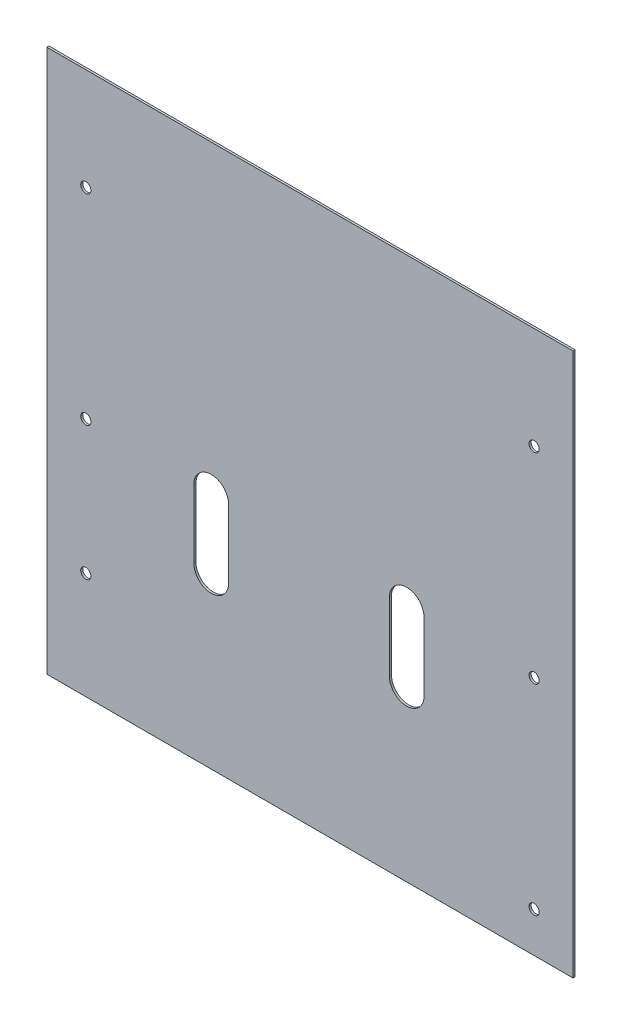
SolidWorks part; units mm, degrees
ref_plane "Front Plane" through (0, 0, 0) normal (0, 0, 1) x (1, 0, 0)
ref_plane "Top Plane" through (0, 0, 0) normal (0, 1, 0) x (1, 0, 0)
ref_plane "Right Plane" through (0, 0, 0) normal (1, 0, 0) x (0, 0, -1)
sketch "Sketch1" plane through (0, 0, 0) normal (0, 0, -1) x (1, 0, 0)
  line L1 (-203.2, 237) -> (-6.35, 237)
  line L2 (-203.2, 237) -> (-203.2, 33.8)
  line L3 (-203.2, 33.8) -> (-6.35, 33.8)
  line L4 (-6.35, 237) -> (-6.35, 33.8)
  dimension "D2" = 196.85
  dimension "D3" = 203.2
extrude "Boss-Extrude1" add sketch "Sketch1" along normal blind 0.7747
sketch "Sketch2" plane through (0, 0, -0.7747) normal (0, 0, -1) x (1, 0, 0)
  line L0 (-141.7213, 180) -> (-141.7213, 141.5) construction
  line L1 (-6.35, 237) -> (-203.2, 237) construction
  line L2 (-141.7213, 180) -> (-141.7213, 237) construction
  line L3 (-141.7213, 173.5) -> (-141.7213, 148) construction
  line L6 (-135.2213, 173.5) -> (-135.2213, 148)
  line L7 (-148.2213, 173.5) -> (-148.2213, 148)
  line L8 (-141.7213, 160.75) -> (-203.2, 160.75) construction
  line L9 (-203.2, 237) -> (-203.2, 33.8) construction
  line L10 (-68.5693, 180) -> (-68.5693, 141.5) construction
  line L11 (-68.5693, 180) -> (-68.5693, 237) construction
  line L12 (-68.5693, 173.5) -> (-68.5693, 148) construction
  line L15 (-141.7213, 160.75) -> (-68.5693, 160.75) construction
  line L16 (-62.0693, 173.5) -> (-62.0693, 148)
  line L17 (-75.0693, 173.5) -> (-75.0693, 148)
  arc A2 (-135.2213, 173.5) -> (-148.2213, 173.5) centre (-141.7213, 173.5) ccw
  arc A3 (-148.2213, 148) -> (-135.2213, 148) centre (-141.7213, 148) ccw
  arc A6 (-62.0693, 173.5) -> (-75.0693, 173.5) centre (-68.5693, 173.5) ccw
  arc A7 (-75.0693, 148) -> (-62.0693, 148) centre (-68.5693, 148) ccw
  point P5 (-141.7213, 160.75)
  point P18 (-68.5693, 160.75)
  dimension "D4" = 6.5
  dimension "D6" = 57
  dimension "D5" = 6.5
  dimension "D1" = 73.152
  dimension "D2" = 57
  dimension "D3" = 38.5
  dimension "D8" = 38.5
extrude "Cut-Extrude7" cut sketch "Sketch2" against normal through all
ref_plane "Plane1" through (-104.775, 0, 0) normal (1, 0, 0) x (0, 0, -1)
sketch "Sketch4" plane through (0, 0, 0) normal (0, 0, 1) x (1, 0, 0)
  line L0 (-203.2, -33.8) -> (-6.35, -33.8) construction
  line L1 (-6.35, -33.8) -> (-203.2, -33.8)
  line L2 (-6.35, -33.8) -> (-6.35, -34.4096)
  line L3 (-6.35, -34.4096) -> (-203.2, -34.4096)
  line L4 (-203.2, -33.8) -> (-203.2, -34.4096)
  line L5 (-6.35, -237) -> (-6.35, 2) construction
  line L6 (-203.2, 2) -> (-203.2, -237) construction
  dimension "D1" = 0.6096
extrude "Boss-Extrude2" add sketch "Sketch4" along normal blind 12
sketch "Sketch8" plane through (0, 0, -0.7747) normal (0, 0, -1) x (-1, 0, 0)
  circle A0 centre (185.47, -222) radius 3.75
  circle A1 centre (185.47, -197) radius 3.75
  circle A2 centre (185.47, -172) radius 3.75
  circle A3 centre (185.47, -147) radius 3.75
  circle A4 centre (185.47, -122) radius 3.75
  circle A5 centre (185.47, -97) radius 3.75
  dimension "D1" = 7.5
sketch "Sketch13" plane through (0, 0, 12) normal (0, 0, 1) x (1, 0, 0)
  line L1 (-6.35, -34.4096) -> (-203.2, -34.4096)
  line L2 (-6.35, -34.4096) -> (-6.35, -33.8)
  line L3 (-6.35, -33.8) -> (-203.2, -33.8)
  line L4 (-203.2, -34.4096) -> (-203.2, -33.8)
sketch "Sketch14" plane through (0, 0, 0) normal (0, 0, 1) x (1, 0, 0)
  line L0 (-6.35, -34.4096) -> (-6.35, -237) construction
  line L1 (-6.35, -59.904) -> (-203.2, -59.904)
  line L2 (-6.35, -59.904) -> (-6.35, -47.966)
  line L3 (-6.35, -47.966) -> (-203.2, -47.966)
  line L4 (-203.2, -59.904) -> (-203.2, -47.966)
  line L5 (-203.2, -237) -> (-203.2, -34.4096) construction
  dimension "D1" = 11.938
extrude "Boss-Extrude3" add sketch "Sketch14" against normal up to surface (0.7747 mm away) up to face at (-141.7213, -160.75, -0.7747)
extrude "Cut-Extrude9" cut sketch "Sketch13" against normal up to surface (12 mm away) up to face at (-68.5693, -160.75, 0)
hole_wizard "CSK for M3 Flat Head Machine Screw3" positions "Sketch15" profile "Sketch16" tap size "M4x0.7" standard "ANSI Metric" end condition through all
sketch "Sketch15" plane through (0, 0, 0) normal (0, 0, 1) x (1, 0, 0)
  point P18 (-188.645, -72)
  point P21 (-188.645, -222)
  point P24 (-188.645, -197)
  point P27 (-188.645, -172)
  point P30 (-188.645, -147)
  point P33 (-188.645, -122)
  point P36 (-188.645, -97)
  point P39 (-188.645, -72)
sketch "Sketch16" plane through (-188.645, -72, 0) normal (1, 0, 0) x (0, -1, 0)
  line L0 (0, 0) -> (0, 0.7747)
  line L1 (0, 0.7747) -> (1.905, 0.7747)
  line L2 (1.905, 0.7747) -> (1.905, 0)
  line L5 (1.905, 0) -> (0, 0)
  line L11 (0, -6.35) -> (0, 107.95) construction
  dimension "Thru Tap Drill Dia." = 3.81
  dimension "Thru Tap Drill Depth" = 0.7747
ref_plane "Plane2" through (-104.775, 0, 0) normal (1, 0, 0) x (0, 0, -1)
mirror "Mirror1" about plane through (-104.775, 0, 0) normal (1, 0, 0) of "CSK for M3 Flat Head Machine Screw3"
sketch "Sketch17" plane through (0, 0, -0.7747) normal (0, 0, -1) x (-1, 0, 0)
  line L0 (62.0693, -148) -> (62.0693, -173.5) construction
  point P8 (141.7213, -160.75)
  point P17 (68.5693, -160.75)
  dimension "D1" = 6.5
  dimension "D2" = 79.652
  dimension "D3" = 12.75
sketch "Sketch19" plane through (0, 0, -0.7747) normal (0, 0, -1) x (-1, 0, 0)
  line L6 (9.9285, -126.7081) -> (192.6049, -126.7081)
  line L7 (9.9285, -126.7081) -> (9.9285, -92.9669)
  line L8 (9.9285, -92.9669) -> (192.6049, -92.9669)
  line L9 (192.6049, -126.7081) -> (192.6049, -92.9669)
extrude "Boss-Extrude4" add sketch "Sketch19" against normal up to surface (0.7747 mm away) up to face at (-19, -222, 0)
sketch "Sketch21" plane through (0, 0, -0.7747) normal (0, 0, -1) x (-1, 0, 0)
  line L1 (174.2127, -182.0755) -> (196.9307, -182.0755)
  line L2 (13.502, -182.0755) -> (35.0408, -182.0755)
  line L3 (13.502, -182.0755) -> (13.502, -165.4323)
  line L4 (13.502, -165.4323) -> (35.0408, -165.4323)
  line L5 (35.0408, -182.0755) -> (35.0408, -165.4323)
  line L6 (174.2127, -182.0755) -> (174.2127, -159.7632)
  line L7 (174.2127, -159.7632) -> (196.9307, -159.7632)
  line L8 (196.9307, -182.0755) -> (196.9307, -159.7632)
extrude "Boss-Extrude5" add sketch "Sketch21" against normal up to surface (0.7747 mm away) up to face at (-19, -222, 0)
sketch "Sketch22" plane through (0, 0, 0) normal (0, 0, 1) x (1, 0, 0)
  line L1 (-182.3612, -227.9915) -> (-196.2665, -227.9915)
  line L2 (-17.4152, -202.4142) -> (-29.9248, -202.4142)
  line L3 (-17.4152, -202.4142) -> (-17.4152, -193.3386)
  line L4 (-17.4152, -193.3386) -> (-29.9248, -193.3386)
  line L5 (-29.9248, -202.4142) -> (-29.9248, -193.3386)
  line L6 (-182.3612, -227.9915) -> (-182.3612, -213.7762)
  line L7 (-182.3612, -213.7762) -> (-196.2665, -213.7762)
  line L8 (-196.2665, -227.9915) -> (-196.2665, -213.7762)
extrude "Boss-Extrude6" add sketch "Sketch22" against normal up to surface (0.7747 mm away) up to face at (-19, -222, -0.7747)
